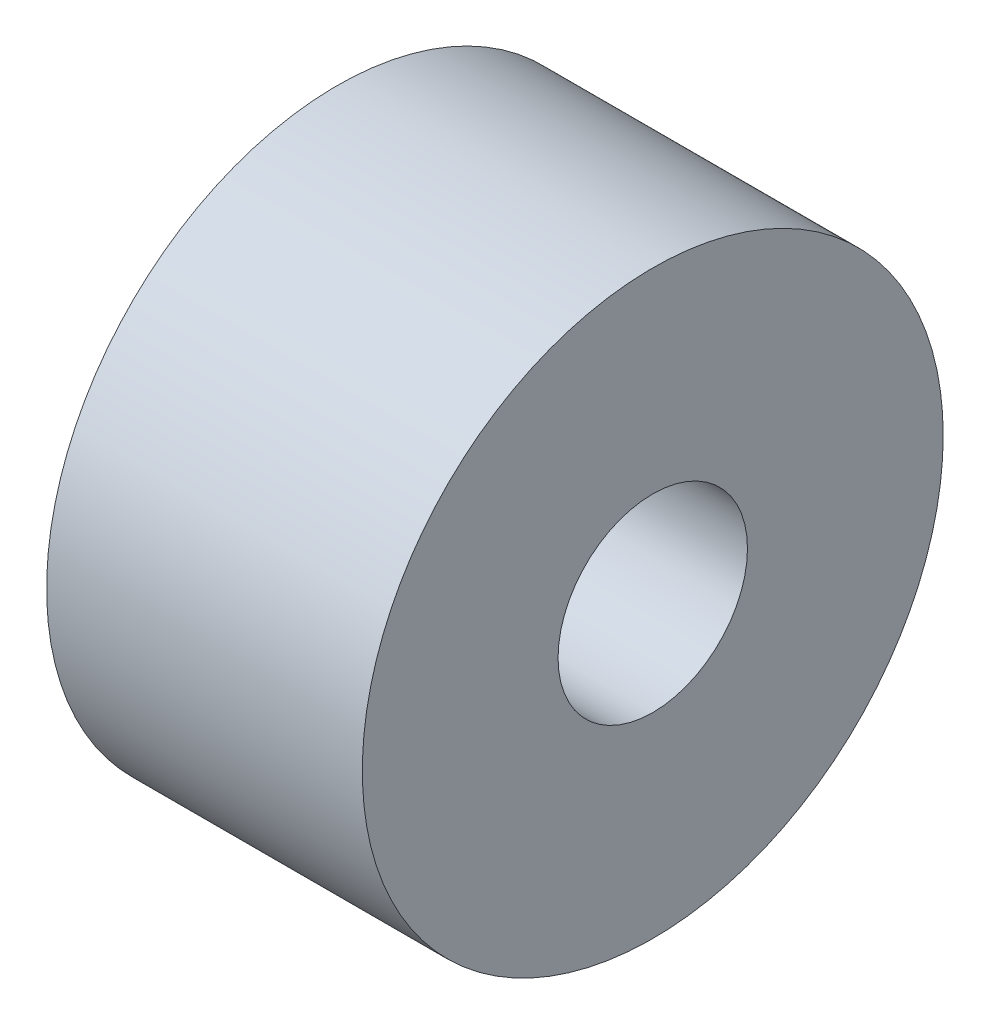
SolidWorks part; units mm, degrees
ref_plane "Front Plane" through (0, 0, 0) normal (0, 0, 1) x (1, 0, 0)
ref_plane "Top Plane" through (0, 0, 0) normal (0, 1, 0) x (1, 0, 0)
ref_plane "Right Plane" through (0, 0, 0) normal (1, 0, 0) x (0, 0, -1)
sketch "Sketch1" plane through (0, 0, 0) normal (1, 0, 0) x (0, 0, -1)
  circle A0 centre (0, 0) radius 4.6
  circle A1 centre (0, 0) radius 1.5
extrude "Boss-Extrude1" add sketch "Sketch1" along normal blind 5
